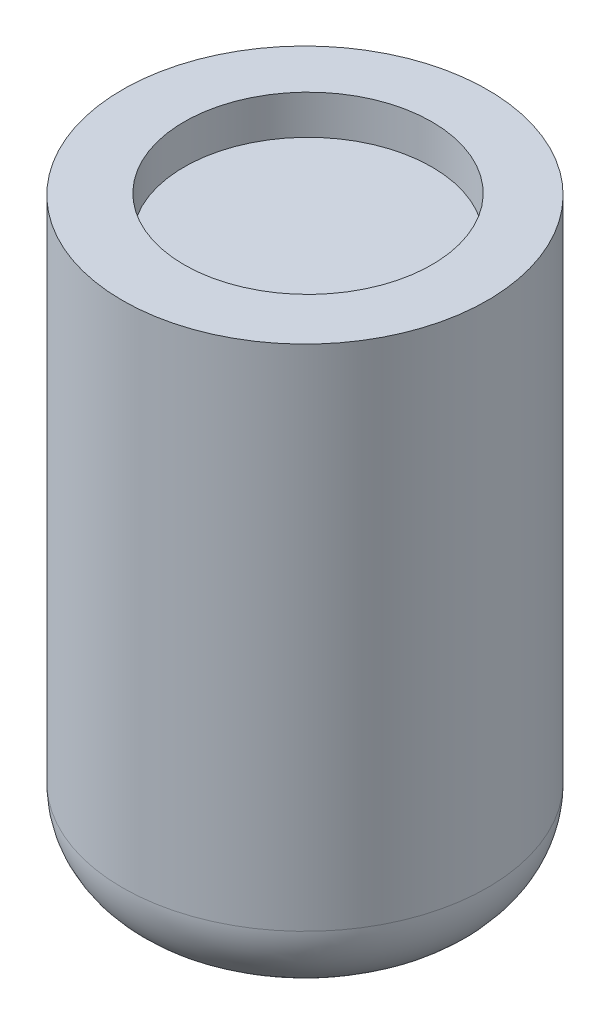
SolidWorks part; units mm, degrees
ref_plane "Спереди" through (0, 0, 0) normal (0, 0, 1) x (1, 0, 0)
ref_plane "Сверху" through (0, 0, 0) normal (0, 1, 0) x (1, 0, 0)
ref_plane "Справа" through (0, 0, 0) normal (1, 0, 0) x (0, 0, -1)
other "Configuration Table"
sketch "Эскиз1" plane through (0, 0, 0) normal (0, 1, 0) x (1, 0, 0)
  circle A0 centre (0, 0) radius 2.8
  dimension "D1" = 5.6
extrude "Бобышка-Вытянуть1" add sketch "Эскиз1" along normal blind 9
sketch "Эскиз2" plane through (0, 9, 0) normal (0, 1, 0) x (1, 0, 0)
  line L0 (0, 2.8) -> (0, -2.8) construction
  line L1 (-2.9393, 0) -> (2.8, 0) construction
  circle A0 centre (0, 0) radius 2.8 construction
  circle A1 centre (0, 0.0472) radius 1.9
  dimension "D1" = 3.8
extrude "Вырез-Вытянуть1" cut sketch "Эскиз2" against normal blind 0.6
fillet "Скругление1" radius 1.2 1 edges at (0, 0, 2.8)
